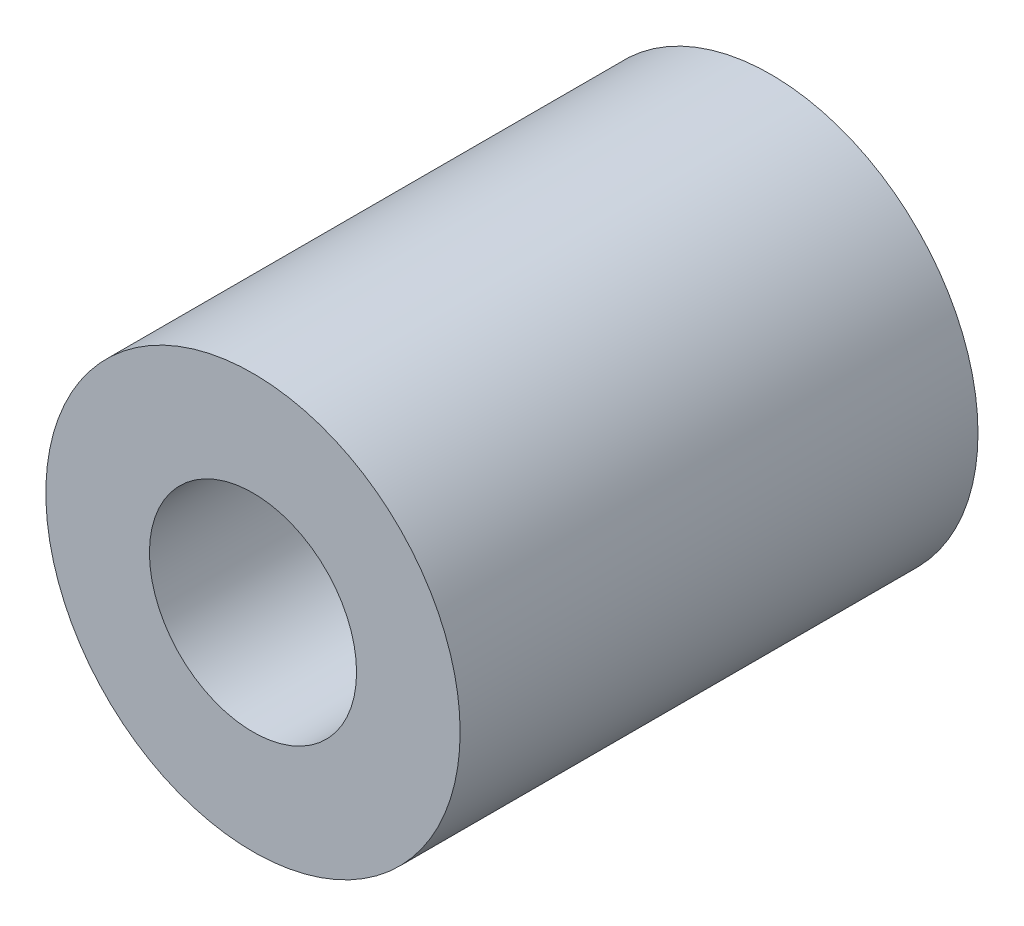
SolidWorks part; units mm, degrees
ref_plane "Спереди" through (0, 0, 0) normal (0, 0, 1) x (1, 0, 0)
ref_plane "Сверху" through (0, 0, 0) normal (0, 1, 0) x (1, 0, 0)
ref_plane "Справа" through (0, 0, 0) normal (1, 0, 0) x (0, 0, -1)
sketch "Эскиз1" plane through (0, 0, 0) normal (0, 0, 1) x (1, 0, 0)
  arc A1 (12, 0) -> (-12, 0) centre (0, 0) ccw
  arc A2 (-12, 0) -> (12, 0) centre (0, 0) ccw
  circle A3 centre (0, 0) radius 6
extrude "Бобышка-Вытянуть1" add sketch "Эскиз1" along normal blind 30
